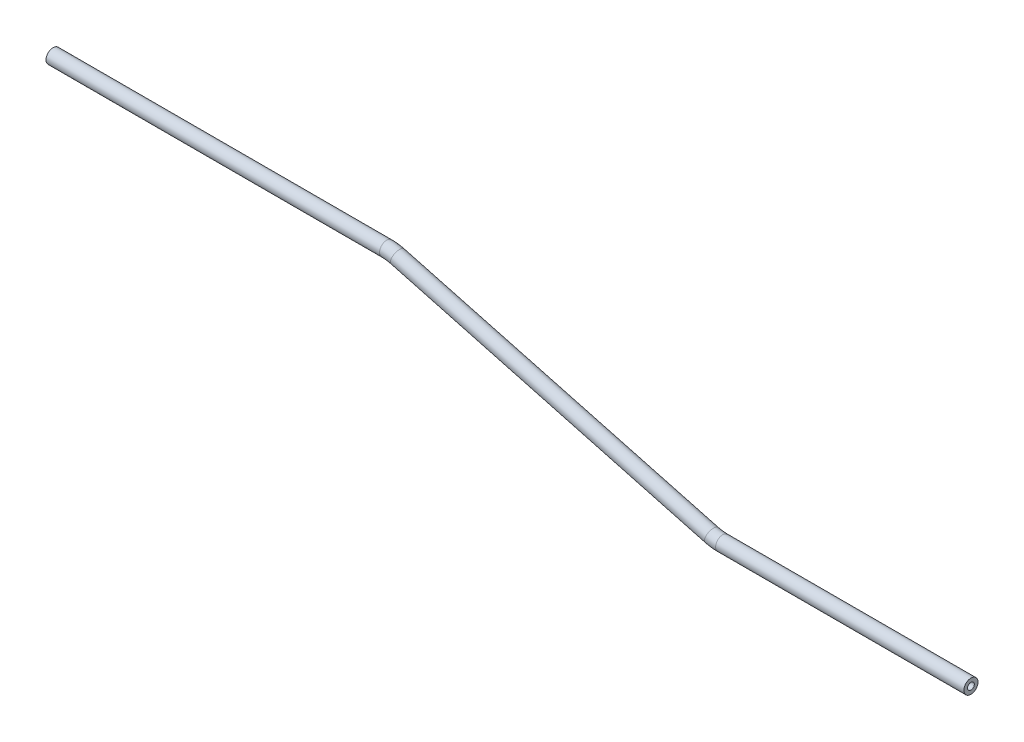
SolidWorks part; units mm, degrees
material "6061 Alloy"
ref_plane "Front Plane" through (0, 0, 0) normal (0, 0, 1) x (1, 0, 0)
ref_plane "Top Plane" through (0, 0, 0) normal (0, 1, 0) x (1, 0, 0)
ref_plane "Right Plane" through (0, 0, 0) normal (1, 0, 0) x (0, 0, -1)
sketch "Sketch1" plane through (0, 0, 0) normal (0, 0, 1) x (1, 0, 0)
  line L0 (-134.9558, 7.1638) -> (14.9363, 7.1638)
  line L1 (19.8668, 6.5146) -> (161.0045, -31.3031)
  line L2 (165.935, -31.9522) -> (277.4811, -31.9522)
  line L3 (161.0045, -31.3031) -> (19.8668, 6.5146) construction
  line L4 (19.8668, 6.5146) -> (-57.951, 27.3659) construction
  line L5 (-57.951, 27.3659) -> (161.0045, -31.3031) construction
  line L6 (161.0045, -31.3031) -> (147.3265, -27.6381) construction
  line L7 (-134.9558, 7.1638) -> (79.5776, 7.1638) construction
  line L8 (277.4811, -31.9522) -> (71.0883, -31.9522) construction
  arc A0 (14.9363, 7.1638) -> (19.8668, 6.5146) centre (14.9363, -11.8862) cw
  arc A1 (161.0045, -31.3031) -> (165.935, -31.9522) centre (165.935, -12.9022) ccw
  point P7 (17.4442, 7.1638)
  point P13 (163.4271, -31.9522)
  dimension "D5" = 19.05
  dimension "D6" = 19.05
  dimension "D1" = 152.4
  dimension "D2" = 151.1325
  dimension "D3" = 114.0541
  dimension "D4" = 15
  dimension "D7" = 15
ref_plane "Plane1" through (-134.9558, 7.1638, 0) normal (1, 0, 0) x (0, 0, -1)
sketch "Sketch2" plane through (-134.9558, 7.1638, 0) normal (1, 0, 0) x (0, 0, -1)
  circle A0 centre (0, 0) radius 3.175
  circle A1 centre (0, 0) radius 1.524
  dimension "D1" = 3.048
  dimension "D2" = 6.35
sweep "Sweep1" add profiles "Sketch2" path "Sketch1"
sketch "Sketch3" plane through (-134.9558, 0, 0) normal (-1, 0, 0) x (0, 0, 1)
  line L0 (-3.175, 7.1638) -> (3.175, 7.1638) construction
  circle A0 centre (0, 7.1638) radius 3.175 construction
sketch "Sketch4" plane through (0, 0, 0) normal (0, 0, 1) x (1, 0, 0)
  line L0 (-134.9558, 7.1638) -> (-137.0301, 7.1638) construction
  line L1 (-134.9558, 10.3388) -> (-134.9558, 3.9888) construction
